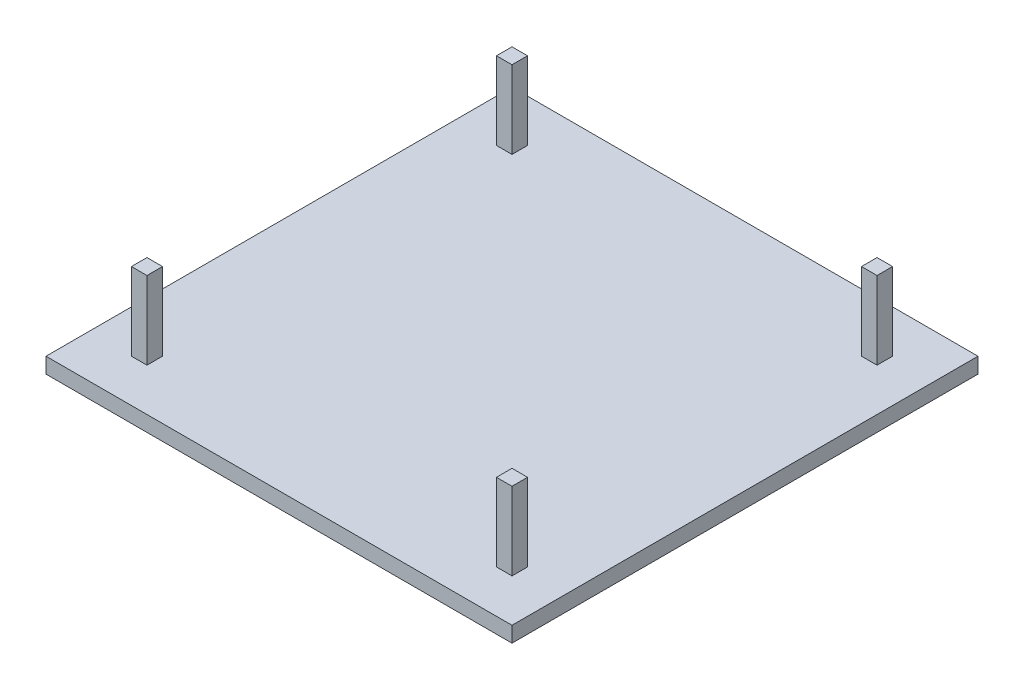
SolidWorks part; units mm, degrees
ref_plane "Front Plane" through (0, 0, 0) normal (0, 0, 1) x (1, 0, 0)
ref_plane "Top Plane" through (0, 0, 0) normal (0, 1, 0) x (1, 0, 0)
ref_plane "Right Plane" through (0, 0, 0) normal (1, 0, 0) x (0, 0, -1)
sketch "Sketch1" plane through (0, 0, 0) normal (0, 1, 0) x (1, 0, 0)
  line L1 (-25.0674, 21.159) -> (34.9326, 21.159)
  line L2 (-25.0674, 21.159) -> (-25.0674, -38.841)
  line L3 (-25.0674, -38.841) -> (34.9326, -38.841)
  line L4 (34.9326, 21.159) -> (34.9326, -38.841)
  dimension "D1" = 60
  dimension "D2" = 60
extrude "Boss-Extrude1" add sketch "Sketch1" along normal blind 2
sketch "Sketch2" plane through (0, 2, 0) normal (0, 1, 0) x (1, 0, 0)
  line L1 (-19.5674, 15.659) -> (-17.5674, 15.659)
  line L2 (-19.5674, 15.659) -> (-19.5674, 13.659)
  line L3 (-19.5674, 13.659) -> (-17.5674, 13.659)
  line L4 (-17.5674, 15.659) -> (-17.5674, 13.659)
  line L14 (4.9326, 21.159) -> (4.9326, -38.841) construction
  line L15 (34.9326, -8.841) -> (-25.0674, -8.841) construction
  line L16 (27.4326, 15.659) -> (27.4326, 13.659)
  line L17 (29.4326, 13.659) -> (27.4326, 13.659)
  line L18 (29.4326, 15.659) -> (29.4326, 13.659)
  line L19 (29.4326, 15.659) -> (27.4326, 15.659)
  line L20 (29.4326, -33.341) -> (27.4326, -33.341)
  line L21 (29.4326, -33.341) -> (29.4326, -31.341)
  line L22 (29.4326, -31.341) -> (27.4326, -31.341)
  line L23 (27.4326, -33.341) -> (27.4326, -31.341)
  line L24 (-17.5674, -33.341) -> (-17.5674, -31.341)
  line L25 (-19.5674, -31.341) -> (-17.5674, -31.341)
  line L26 (-19.5674, -33.341) -> (-19.5674, -31.341)
  line L27 (-19.5674, -33.341) -> (-17.5674, -33.341)
  line L28 (-25.0674, -38.841) -> (34.9326, -38.841) construction
  line L29 (34.9326, 21.159) -> (-25.0674, 21.159) construction
  line L30 (34.9326, -38.841) -> (34.9326, 21.159) construction
  line L31 (-25.0674, 21.159) -> (-25.0674, -38.841) construction
  point P29 (-18.5674, -31.341)
  point P35 (4.9326, -38.841)
  point P36 (34.9326, -8.841)
  dimension "D1" = 2
  dimension "D2" = 2
  dimension "D3" = 45
  dimension "D4" = 45
extrude "Boss-Extrude2" add sketch "Sketch2" along normal blind 10
